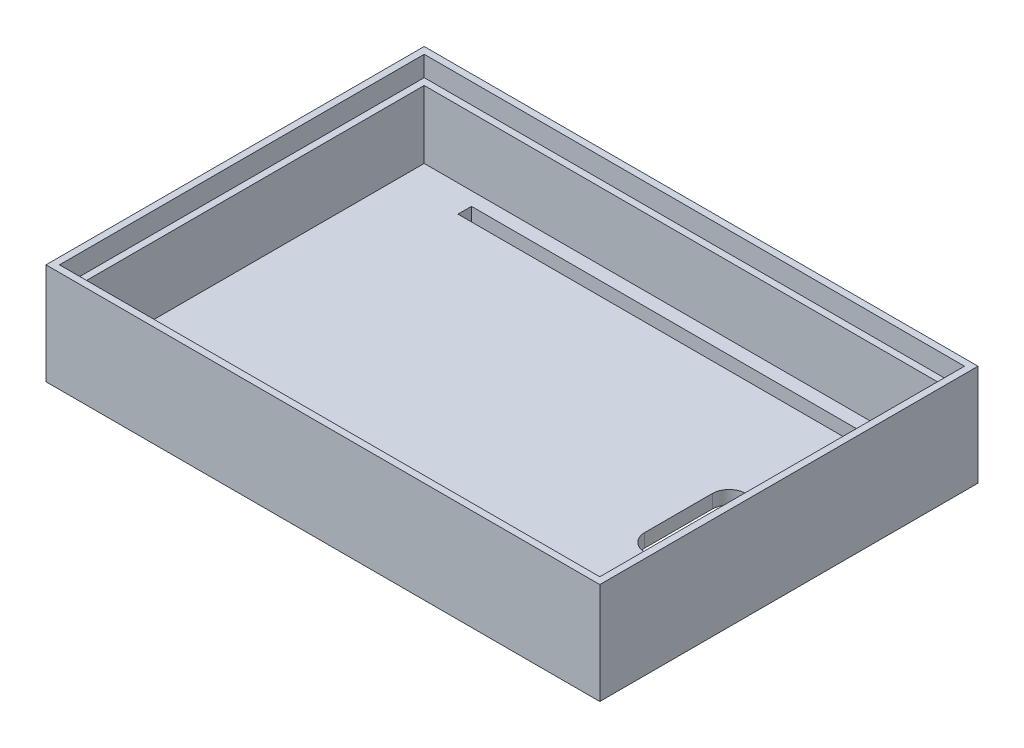
SolidWorks part; units mm, degrees
ref_plane "Front Plane" through (0, 0, 0) normal (0, 0, 1) x (1, 0, 0)
ref_plane "Top Plane" through (0, 0, 0) normal (0, 1, 0) x (1, 0, 0)
ref_plane "Right Plane" through (0, 0, 0) normal (1, 0, 0) x (0, 0, -1)
sketch "Sketch1" plane through (0, 0, 0) normal (0, 1, 0) x (1, 0, 0)
  line L1 (0, 0) -> (82, 0)
  line L2 (0, 0) -> (0, 56)
  line L3 (0, 56) -> (82, 56)
  line L4 (82, 0) -> (82, 56)
  dimension "D1" = 82
  dimension "D2" = 56
extrude "Boss-Extrude1" add sketch "Sketch1" along normal blind 15
sketch "Sketch3" plane through (0, 15, 0) normal (0, 1, 0) x (1, 0, 0)
  line L0 (0, 56) -> (0, 0) construction
  line L1 (1, 55) -> (81, 55)
  line L2 (1, 55) -> (1, 1)
  line L3 (1, 1) -> (81, 1)
  line L4 (81, 55) -> (81, 1)
  line L5 (82, 0) -> (82, 56) construction
  line L6 (82, 56) -> (0, 56) construction
  line L7 (0, 0) -> (82, 0) construction
  dimension "D1" = 1
  dimension "D2" = 1
  dimension "D3" = 1
  dimension "D4" = 1
extrude "Cut-Extrude1" cut sketch "Sketch3" against normal blind 3
sketch3d "3DSketch1"
  line L0 (80, 12, -2) -> (80, 12, -54)
  line L1 (80, 12, -54) -> (2, 12, -54)
  line L2 (2, 12, -54) -> (2, 12, -2)
  line L3 (2, 12, -2) -> (80, 12, -2)
  line L4 (80, 12, -2) -> (80, 12, -54)
  line L5 (80, 12, -54) -> (2, 12, -54)
  line L6 (2, 12, -54) -> (2, 12, -2)
  line L7 (2, 12, -2) -> (80, 12, -2)
  dimension "D1" = 1
extrude "Cut-Extrude2" cut sketch "3DSketch1" along direction (0, 1, 0) on the side against the normal blind 10
sketch "Sketch5" plane through (0, 0, 0) normal (0, -1, 0) x (1, 0, 0)
  line L0 (0, 0) -> (82, 0) construction
  line L1 (11, -4) -> (71, -4)
  line L2 (11, -4) -> (11, -6)
  line L3 (11, -6) -> (71, -6)
  line L4 (71, -4) -> (71, -6)
  line L5 (0, -56) -> (0, 0) construction
  line L6 (0, -28) -> (82, -28) construction
  line L7 (82, 0) -> (82, -56) construction
  line L8 (11, -50) -> (71, -50)
  line L9 (71, -52) -> (71, -50)
  line L10 (11, -52) -> (71, -52)
  line L11 (11, -52) -> (11, -50)
  line L12 (68.1538, -23) -> (68.1538, -33) construction
  line L13 (70.6538, -23) -> (70.6538, -25.5)
  line L14 (65.6538, -23) -> (65.6538, -33)
  line L15 (70.6538, -30.5) -> (70.6538, -33)
  arc A0 (70.6538, -23) -> (65.6538, -23) centre (68.1538, -23) ccw
  arc A1 (65.6538, -33) -> (70.6538, -33) centre (68.1538, -33) ccw
  arc A2 (70.6538, -25.5) -> (70.6538, -30.5) centre (70.6538, -28) cw
  point P8 (41, -4)
  point P19 (68.1538, -28)
  point P24 (68.1538, -20.5)
  point P25 (68.1538, -35.5)
  dimension "D7" = 2.5
  dimension "D1" = 60
  dimension "D2" = 2
  dimension "D3" = 41
  dimension "D4" = 4
  dimension "D5" = 5
  dimension "D6" = 15
extrude "Cut-Extrude3" cut sketch "Sketch5" against normal blind 11
